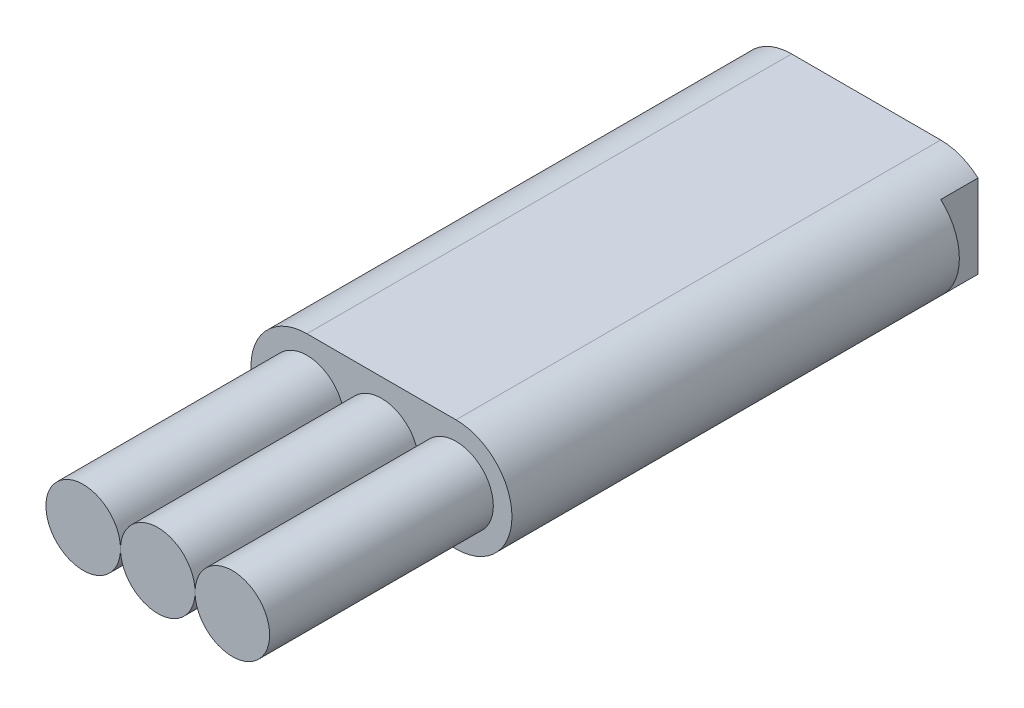
SolidWorks part; units mm, degrees
ref_plane "Спереди" through (0, 0, 0) normal (0, 0, 1) x (1, 0, 0)
ref_plane "Сверху" through (0, 0, 0) normal (0, 1, 0) x (1, 0, 0)
ref_plane "Справа" through (0, 0, 0) normal (1, 0, 0) x (0, 0, -1)
sketch "Эскиз1" plane through (0, 0, 0) normal (0, 0, 1) x (1, 0, 0)
  circle A0 centre (0, 0) radius 1
  circle A1 centre (-2, 0) radius 1
  circle A2 centre (2, 0) radius 1
  dimension "D1" = 2
  dimension "D2" = 2
  dimension "D3" = 2
extrude "Бобышка-Вытянуть1" add sketch "Эскиз1" along normal blind 6 contours A1 | A0 | A2
sketch "Эскиз2" plane through (0, 0, 0) normal (0, 0, -1) x (-1, 0, 0)
  line L0 (-2, 0) -> (2, 0) construction
  line L1 (-2, 1.5) -> (2, 1.5)
  line L2 (-2, -1.5) -> (2, -1.5)
  arc A0 (-2, 1.5) -> (-2, -1.5) centre (-2, 0) ccw
  arc A1 (2, -1.5) -> (2, 1.5) centre (2, 0) ccw
  point P2 (0, 0)
  dimension "D1" = 1.5
extrude "Бобышка-Вытянуть5" add sketch "Эскиз2" along normal blind 13 separate body
sketch "Эскиз3" plane through (0, 0, -13) normal (0, 0, -1) x (-1, 0, 0)
  line L1 (4.3641, 3.034) -> (3, 3.034)
  line L2 (4.3641, 3.034) -> (4.3641, -3.3698)
  line L3 (4.3641, -3.3698) -> (3, -3.3698)
  line L4 (3, 3.034) -> (3, -3.3698)
  line L5 (-5.2405, -2.3851) -> (-3, -2.3851)
  line L6 (-5.2405, -2.3851) -> (-5.2405, 3.034)
  line L7 (-5.2405, 3.034) -> (-3, 3.034)
  line L8 (-3, -2.3851) -> (-3, 3.034)
  dimension "D1" = 3
  dimension "D2" = 3
extrude "Вырез-Вытянуть1" cut sketch "Эскиз3" against normal blind 1
